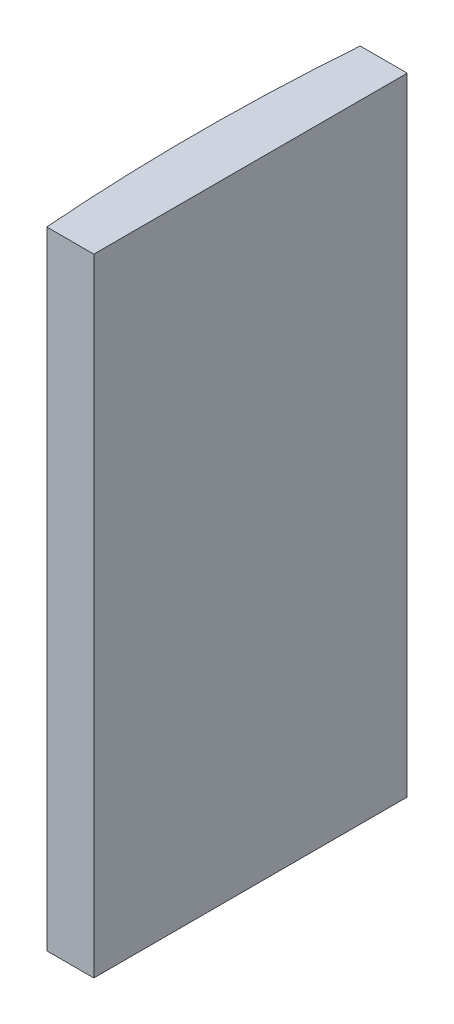
SolidWorks part; units mm, degrees
ref_plane "前视基准面" through (0, 0, 0) normal (0, 0, 1) x (1, 0, 0)
ref_plane "上视基准面" through (0, 0, 0) normal (0, 1, 0) x (1, 0, 0)
ref_plane "右视基准面" through (0, 0, 0) normal (1, 0, 0) x (0, 0, -1)
sketch "草图1" plane through (0, 0, 0) normal (0, 1, 0) x (1, 0, 0)
  line L0 (10.7432, 0) -> (-607.0701, 0) construction
  line L1 (-124.5074, 10) -> (-121.5048, 10)
  line L2 (-124.5074, -10) -> (-121.5048, -10)
  line L3 (-121.5048, 10) -> (-121.5048, -10)
  arc A0 (-124.5074, 10) -> (-124.5074, -10) centre (4.3552, 0) ccw
  point P19 (-124.8948, 0)
  point P20 (-121.5048, 0)
  dimension "D2" = 10
  dimension "D3" = 129.25
  dimension "D4" = 3.39
  dimension "D1" = 10
extrude "凸台-拉伸1" add sketch "草图1" along normal blind 40
